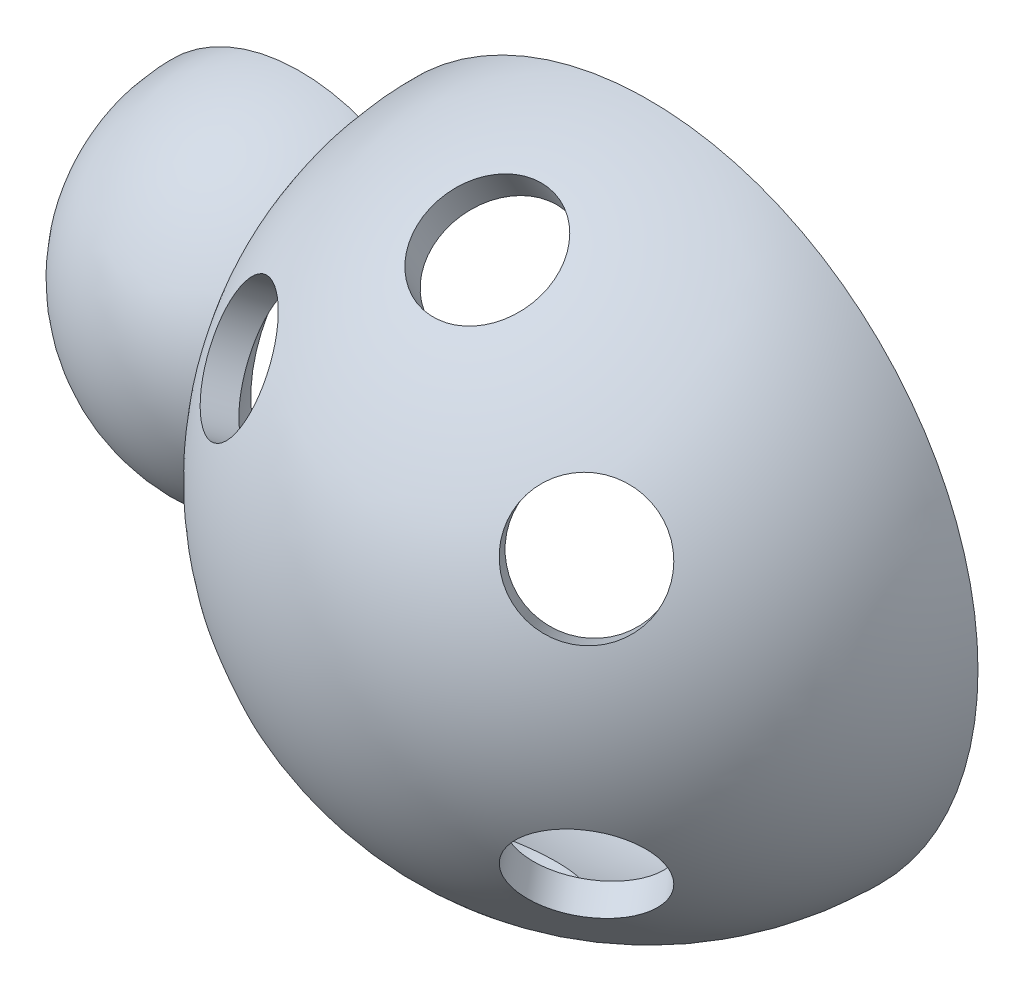
SolidWorks part; units mm, degrees
ref_plane "Front Plane" through (0, 0, 0) normal (0, 0, 1) x (1, 0, 0)
ref_plane "Top Plane" through (0, 0, 0) normal (0, 1, 0) x (1, 0, 0)
ref_plane "Right Plane" through (0, 0, 0) normal (1, 0, 0) x (0, 0, -1)
sketch "Sketch1" plane through (0, 0, 0) normal (0, 0, 1) x (1, 0, 0)
  line L0 (-106, 0) -> (-100, 0)
  line L1 (60, 0) -> (66, 0)
  arc A0 (-54.2857, 25.5551) -> (60, 0) centre (0, 0) cw
  arc A1 (-56.8571, 33.5152) -> (66, 0) centre (0, 0) cw
  arc A2 (-54.2857, 25.5551) -> (-100, 0) centre (-70, 0) ccw
  arc A3 (-56.8571, 33.5152) -> (-106, 0) centre (-70, 0) ccw
  point P9 (0, 0)
  point P10 (-54.5672, 24.9484)
  dimension "D1" = 30
  dimension "D2" = 60
  dimension "D3" = 6
  dimension "D4" = 70
revolve "Revolve1" add sketch "Sketch1" angle 180 about L0
sketch3d "3DSketch1"
  line L0 (0, 0, 0) -> (81.9642, 0, 0)
ref_plane "Plane1" through (0, 0, 0) normal (0, -0.866, 0.5) x (1, 0, 0)
sketch "Sketch2" plane through (0, 0, 0) normal (0, -0.866, 0.5) x (1, 0, 0)
  line L0 (0, 0) -> (39.8154, -62.4976)
  line L1 (0, 0) -> (-39.8154, -62.4976)
  point P3 (0, 0)
  point P5 (43.5014, 59.9904)
  dimension "D1" = 65
ref_plane "spot Plane" through (-35.4618, 27.8319, 48.2063) normal (-0.5373, 0.4217, 0.7304) x (0.8338, 0.3957, 0.385)
sketch "Sketch3" plane through (-35.4618, 27.8319, 48.2063) normal (-0.5373, 0.4217, 0.7304) x (0.8338, 0.3957, 0.385)
  circle A0 centre (0, 0) radius 12.5
  dimension "D1" = 25
extrude "Spot1" cut sketch "Sketch3" against normal blind 10
ref_plane "Plane3" through (35.4618, 27.8319, 48.2063) normal (0.5373, 0.4217, 0.7304) x (0.8434, -0.2686, -0.4653)
sketch "Sketch4" plane through (35.4618, 27.8319, 48.2063) normal (0.5373, 0.4217, 0.7304) x (0.8434, -0.2686, -0.4653)
  circle A0 centre (0, 0) radius 12.5
  dimension "D1" = 25
extrude "Spot2" cut sketch "Sketch4" against normal blind 10
ref_plane "Plane4" through (0, 0, 0) normal (0, -0.5, 0.866) x (1, 0, 0)
sketch "Sketch5" plane through (0, 0, 0) normal (0, -0.5, 0.866) x (1, 0, 0)
  line L0 (0, 0) -> (0, 97.2732)
ref_plane "Plane5" through (0, 57.1577, 33) normal (0, 0.866, 0.5) x (1, 0, 0)
sketch "Sketch6" plane through (0, 57.1577, 33) normal (0, 0.866, 0.5) x (1, 0, 0)
  circle A0 centre (0, 0) radius 12.5
  dimension "D1" = 25
extrude "Spot3" cut sketch "Sketch6" against normal blind 10
mirror "Mirror1" about plane through (0, 0, 0) normal (0, 1, 0) of "Spot3", "Spot2", "Spot1"
sketch "Sketch7" plane through (0, 0, 0) normal (1, 0, 0) x (0, 0, -1)
  line L2 (0, 6.35) -> (-8.5, 6.35)
  line L3 (0, 6.35) -> (0, -6.35)
  line L4 (0, -6.35) -> (-8.5, -6.35)
  line L5 (-8.5, 6.35) -> (-8.5, -6.35)
  point P1 (0, 0)
  point P5 (0, 0)
  dimension "D1" = 12.7
  dimension "D2" = 8.5
extrude "Cut-Extrude4" cut sketch "Sketch7" against normal through all
